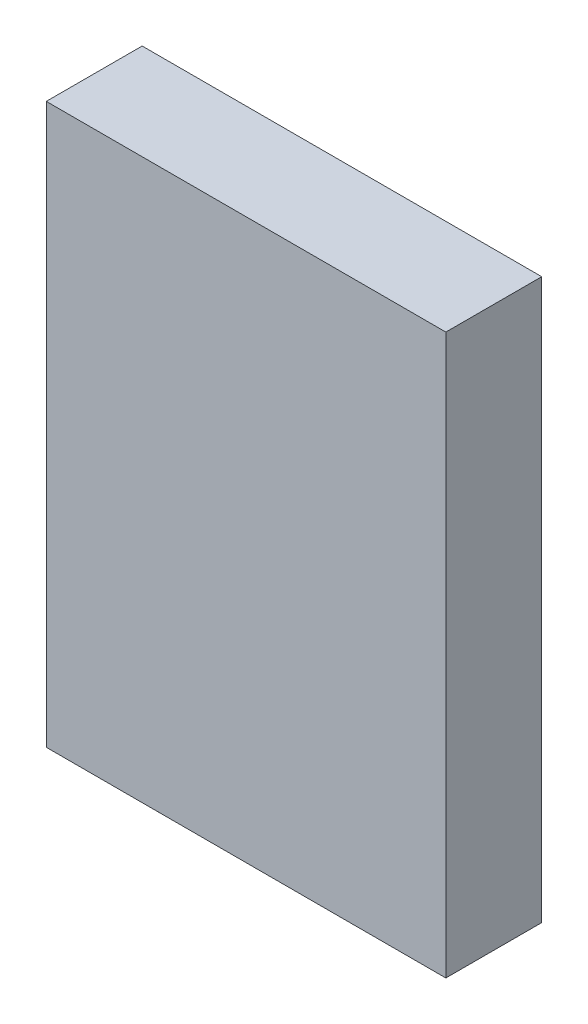
SolidWorks part; units mm, degrees
ref_plane "前视基准面" through (0, 0, 0) normal (0, 0, 1) x (1, 0, 0)
ref_plane "上视基准面" through (0, 0, 0) normal (0, 1, 0) x (1, 0, 0)
ref_plane "右视基准面" through (0, 0, 0) normal (1, 0, 0) x (0, 0, -1)
sketch "草图1" plane through (0, 0, 0) normal (0, 0, 1) x (1, 0, 0)
  line L1 (-6.3516, 7.5203) -> (6.1484, 7.5203)
  line L2 (-6.3516, 7.5203) -> (-6.3516, -9.9797)
  line L3 (-6.3516, -9.9797) -> (6.1484, -9.9797)
  line L4 (6.1484, 7.5203) -> (6.1484, -9.9797)
  dimension "D1" = 12.5
  dimension "D2" = 17.5
extrude "凸台-拉伸1" add sketch "草图1" along normal blind 3
